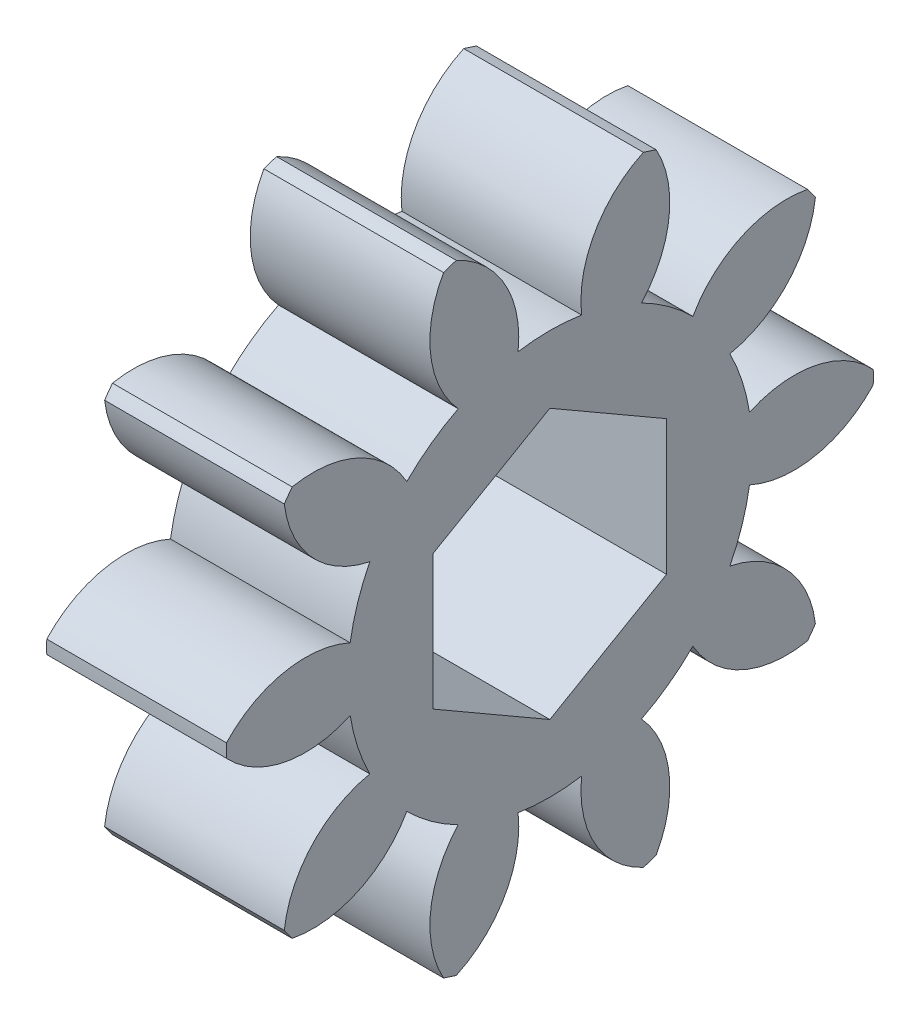
SolidWorks part; units mm, degrees
ref_plane "Plane1" through (0, 0, 0) normal (0, 0, 1) x (1, 0, 0)
ref_plane "Plane2" through (0, 0, 0) normal (0, 1, 0) x (1, 0, 0)
ref_plane "Plane3" through (0, 0, 0) normal (1, 0, 0) x (0, 0, -1)
sketch "HoldingSke" plane through (0, 0, 0) normal (0, 1, 0) x (1, 0, 0)
  line L0 (0, 0) -> (0.6565, -0.1158)
  line L1 (-15, 0) -> (100, 0) construction
  line L2 (0, 0) -> (-2.1039, 2.3779)
  line L3 (0, 0) -> (-11.863, 4.5341)
  line L4 (0, 0) -> (8.5048, 1.4996)
  line L5 (0, 0) -> (-46.8476, -17.4728)
  line L6 (0, 0) -> (-9.9476, -6.7116)
  line L7 (-2.1039, 2.3779) -> (8.6586, 51.2061)
  line L8 (-76.2, 54.61) -> (-75.3, 54.61)
  line L9 (-71.009, 38.7566) -> (-53.1078, 45.2721)
  line L10 (-76.2, 71.12) -> (104.1128, 71.12)
  line L11 (0, 0) -> (-12, 0)
  line L12 (-76.2, 101.6) -> (-76.147, 101.6)
  line L13 (24.9733, 27.94) -> (52.9518, 28.4284)
  line L14 (24.9733, 27.94) -> (24.9743, 27.94)
  line L15 (24.9733, 27.94) -> (100.4006, 29.5858)
  line L16 (-63.627, -1.5) -> (-12.827, -1.5)
  circle A0 centre (0, 0) radius 2.5
  circle A1 centre (0, 0) radius 5.624
  circle A2 centre (0, 0) radius 37.5
  circle A3 centre (0, 0) radius 2.5
  dimension "MHD" = 11.248
  dimension "Hub_dia" = 75
  dimension "Bore" = 5
  dimension "MBD" = 5
  dimension "Num_teeth" = 10
  dimension "Pitch" = 0.6667
  dimension "Overall_len" = 50
  dimension "Show_teeth" = 10
  dimension "Thickness" = 12
  dimension "OAL" = 50.0003
  dimension "T_dim" = 0.9
  dimension "Ap" = 20
  dimension "H" = 19.05
  dimension "Pitch_radius" = 180.3128
  dimension "Width" = 12
  dimension "Backlash" = 0.053
  dimension "Addendum_fac" = 1
  dimension "Dedendum_fac" = 1.25
  dimension "Clearance_fac" = 0.25
  dimension "Dedendum_add" = 0.001
  dimension "Module" = 1.5
sketch "BasProSke" plane through (0, 0, 0) normal (0, 1, 0) x (1, 0, 0)
  line L0 (-10, 0) -> (60, 0) construction
  line L1 (0, 0) -> (0, 9)
  line L2 (0, 0) -> (5, 0)
  line L3 (5, 0) -> (5, 9)
  line L4 (5, 9) -> (0, 9)
  dimension "Thickness" = 5
  dimension "Diameter" = 18
revolve "Base-Revolve" add sketch "BasProSke" angle 360 about L0
sketch "TooCutSke" plane through (0, 0, 0) normal (1, 0, 0) x (0, 0, -1)
  line L1 (0, 0) -> (0, 107) construction
  line L2 (0, 0) -> (-1.2658, 7.3924) construction
  line L3 (0, 0) -> (-4.5869, 14.117) construction
  line L4 (-1.2658, 7.3924) -> (-2.2934, 7.0585) construction
  arc A0 (0.8839, 5.5541) -> (-0.8839, 5.5541) centre (0, 0) ccw
  arc A1 (2.6378, 8.6313) -> (-2.6378, 8.6313) centre (0, 0) ccw
  circle A2 centre (0, 0) radius 7.5 construction
  circle A3 centre (0, 0) radius 7.0477 construction
  arc A4 (-0.8839, 5.5541) -> (-2.6378, 8.6313) centre (-3.8646, 5.8936) ccw
  arc A5 (2.6378, 8.6313) -> (0.8839, 5.5541) centre (3.8646, 5.8936) ccw
  dimension "Root_dia" = 11.248
  dimension "Overcut_dia" = 18.0508
  dimension "Pitch_dia" = 15
  dimension "Base_dia" = 14.0954
  dimension "Flank_rad" = 3
  dimension "Half_ang" = 18
  dimension "Half_CT" = 1.0805
extrude "ToothCut" cut sketch "TooCutSke" along normal through all
fillet "Breaks" [suppressed] radius 0.03
fillet "RootFillets" [suppressed] radius 0.376
pattern_circular "TeethCuts" count 10 every 36 about axis through (-10, 0, 0) along (1, 0, 0) of "ToothCut", "RootFillets", "Breaks"
sketch "HubNeaOneSke" plane through (0, 0, 0) normal (-1, 0, 0) x (0, 0, 1)
  circle A0 centre (0, 0) radius 5.624
  dimension "Diameter" = 11.248
extrude "HubNearOne" [suppressed] add sketch "HubNeaOneSke" along normal blind 45.0003
sketch "HubNeaBotSke" plane through (0, 0, 0) normal (-1, 0, 0) x (0, 0, 1)
  circle A0 centre (0, 0) radius 5.624
  dimension "Diameter" = 11.248
extrude "HubNearBoth" [suppressed] add sketch "HubNeaBotSke" along normal blind 22.5002
ref_plane "FarPln" through (5, 0, 0) normal (1, 0, 0) x (0, 0, -1)
sketch "HubFarSke" plane through (5, 0, 0) normal (1, 0, 0) x (0, 0, -1)
  circle A0 centre (0, 0) radius 5.624
  dimension "Diameter" = 11.248
extrude "HubFar" [suppressed] add sketch "HubFarSke" along normal blind 22.5002
sketch "BorSke" plane through (0, 0, 0) normal (1, 0, 0) x (0, 0, -1)
  line L1 (0, 3.75) -> (-3.2476, 1.875)
  line L2 (-3.2476, 1.875) -> (-3.2476, -1.875)
  line L3 (-3.2476, -1.875) -> (0, -3.75)
  line L4 (0, -3.75) -> (3.2476, -1.875)
  line L5 (3.2476, -1.875) -> (3.2476, 1.875)
  line L6 (3.2476, 1.875) -> (0, 3.75)
  circle A0 centre (0, 0) radius 3.75 construction
  circle A1 centre (0, 0) radius 3.2476 construction
  dimension "Diameter" = 7.5
extrude "Bore" cut sketch "BorSke" along normal mid plane 100.0006
sketch "KeySke" plane through (0, 0, 0) normal (1, 0, 0) x (0, 0, -1)
  line L0 (-1, 0) -> (-1, 3.4)
  line L1 (-1, 3.4) -> (1, 3.4)
  line L2 (1, 3.4) -> (1, 0)
  line L3 (0, 0) -> (0, 34) construction
  line L4 (-1, 0) -> (1, 0)
  dimension "Offset" = 3.4
  dimension "Width" = 2
extrude "Keyway" [suppressed] cut sketch "KeySke" along normal mid plane 100.0006
pattern_circular "Keyway2" [suppressed] count 2 every 90 about axis through (-10, 0, 0) along (1, 0, 0)
equation "' \"Module@HoldingSke\" = 6.35"
equation "' \"Num_teeth@HoldingSke\" = 12"
equation "' \"Ap@HoldingSke\" =  20"
equation "' \"Ap@HoldingSke\" = 20"
equation "' \"Width@HoldingSke\" = 0.5 * 25.4"
equation "' \"Hub_dia@HoldingSke\"= 1 * 25.4"
equation "' \"Hub_dia@HoldingSke\" = 1 * 25.4"
equation "' \"Overall_len@HoldingSke\" = 1.0 * 25.4"
equation "' \"Bore@HoldingSke\" = 0.75 * 25.4"
equation "' \"T_dim@HoldingSke\" = 0.1 * 25.4"
equation "' \"Width@KeySke\" = 0.25 * 25.4"
equation "' \"Show_teeth@HoldingSke\" = 13"
equation "' \"Backlash@HoldingSke\" = 0.009 * 25.4"
equation "' \"Addendum_fac@HoldingSke\" = 1.0"
equation "' \"Dedendum_fac@HoldingSke\" = 1.25"
equation "' \"Dedendum_add@HoldingSke\" = 0.00005 * 25.4"
equation "' \"Clearance_fac@HoldingSke\" = 0.25"
equation "\"Pitch@HoldingSke\" = 1 / \"Module@HoldingSke\""
equation "\"Overcut_dia@TooCutSke\" = (\"Num_teeth@HoldingSke\" + 2 * \"Addendum_fac@HoldingSke\") / \"Pitch@HoldingSke\" + 0.002 * 25.4"
equation "\"Pitch_dia@TooCutSke\" = \"Num_teeth@HoldingSke\" / \"Pitch@HoldingSke\""
equation "\"Base_dia@TooCutSke\" = \"Num_teeth@HoldingSke\" / \"Pitch@HoldingSke\" * cos((\"Ap@HoldingSke\"  * 3.14159265 / 180))"
equation "\"Root_dia@TooCutSke\" = (\"Num_teeth@HoldingSke\" + 2) / \"Pitch@HoldingSke\" - 2 * (\"Addendum_fac@HoldingSke\" + \"Dedendum_fac@HoldingSke\") / \"Pitch@HoldingSke\" - \"Dedendum_add@HoldingSke\" * 2"
equation "\"Half_ang@TooCutSke\" = 180 / \"Num_teeth@HoldingSke\""
equation "\"Half_CT@TooCutSke\" = \"Num_teeth@HoldingSke\" / \"Pitch@HoldingSke\" * sin((3.14159265 / 2 / \"Num_teeth@HoldingSke\")) / 2 - 7 * \"Backlash@HoldingSke\" / 4"
equation "\"Flank_rad@TooCutSke\" = \"Num_teeth@HoldingSke\" / \"Pitch@HoldingSke\" / 5"
equation "\"Radius@RootFillets\" = \"Clearance_fac@HoldingSke\" / \"Pitch@HoldingSke\" + \"Dedendum_add@HoldingSke\""
equation "\"Break_rad@Breaks\" = 0.02 / \"Pitch@HoldingSke\""
equation "\"Thickness@HoldingSke\" = \"Width@HoldingSke\""
equation "\"OAL@HoldingSke\" = \"Thickness@HoldingSke\""
equation "\"MHD@HoldingSke\" = (\"Num_teeth@HoldingSke\" + 2) / \"Pitch@HoldingSke\" - 2 * (\"Addendum_fac@HoldingSke\" + \"Dedendum_fac@HoldingSke\")  / \"Pitch@HoldingSke\" - \"Dedendum_add@HoldingSke\" * 2"
equation "\"MBD@HoldingSke\" = (\"Num_teeth@HoldingSke\" + 2) / \"Pitch@HoldingSke\" - 2 * (\"Addendum_fac@HoldingSke\" + \"Dedendum_fac@HoldingSke\")  / \"Pitch@HoldingSke\" - \"Dedendum_add@HoldingSke\" * 2 - 0.002 * 25.4"
equation "\"MHD@HoldingSke\" = ((sgn( \"MHD@HoldingSke\" - \"Hub_dia@HoldingSke\" )-1)*( \"MHD@HoldingSke\" - \"Hub_dia@HoldingSke\" ))/-2+ \"Hub_dia@HoldingSke\""
equation "\"MBD@HoldingSke\" = ((sgn( \"MBD@HoldingSke\" - \"Bore@HoldingSke\" )-1)*( \"MBD@HoldingSke\" - \"Bore@HoldingSke\" ))/-2+ \"Bore@HoldingSke\""
equation "\"OAL@HoldingSke\" = ((sgn( \"OAL@HoldingSke\" - \"Overall_len@HoldingSke\" )+1)*( \"OAL@HoldingSke\" - \"Overall_len@HoldingSke\" ))/2 + \"Overall_len@HoldingSke\" + 0.000002 * 25.4"
equation "\"Num_teeth@TeethCuts\" = int( \"Show_teeth@HoldingSke\" ) + 1"
equation "\"Num_teeth@TeethCuts\" = ((sgn( \"Num_teeth@TeethCuts\" - \"Num_teeth@HoldingSke\" )-1)*( \"Num_teeth@TeethCuts\" - \"Num_teeth@HoldingSke\" ))/-2+ \"Num_teeth@HoldingSke\""
equation "\"Num_teeth@TeethCuts\" = ((sgn( \"Num_teeth@TeethCuts\" - 2.0)+1)*( \"Num_teeth@TeethCuts\" - 2.0))/2 +2.0"
equation "\"Angle@TeethCuts\" = 360.0 / \"Num_teeth@HoldingSke\""
equation "\"Diameter@BasProSke\" = (\"Num_teeth@HoldingSke\" + 2 * \"Addendum_fac@HoldingSke\") / \"Pitch@HoldingSke\""
equation "' \"Fillet_rad@BasProSke\" =  \"Thickness@HoldingSke\" * 0.05"
equation "' \"Fillet_rad@BasProSke\" = \"Thickness@HoldingSke\" * 0.05"
equation "\"MHD@HoldingSke\" = ((sgn( \"MHD@HoldingSke\" - \"Root_dia@TooCutSke\" )-1)*( \"MHD@HoldingSke\" - \"Root_dia@TooCutSke\" ))/-2+ \"Root_dia@TooCutSke\""
equation "\"Diameter@HubNeaOneSke\" = \"MHD@HoldingSke\""
equation "\"Length@HubNearOne\" = \"OAL@HoldingSke\" - \"Thickness@BasProSke\""
equation "\"Diameter@HubNeaBotSke\" = \"MHD@HoldingSke\""
equation "\"Length@HubNearBoth\" = ( \"OAL@HoldingSke\" - \"Thickness@BasProSke\" ) / 2.0"
equation "\"Thickness@FarPln\" = \"Thickness@BasProSke\""
equation "\"Diameter@HubFarSke\" = \"MHD@HoldingSke\""
equation "\"Length@HubFar\" = ( \"OAL@HoldingSke\" - \"Thickness@BasProSke\" ) / 2.0"
equation "\"Diameter@BorSke\"=7.5"
equation "\"D1@Bore\" = \"OAL@HoldingSke\" * 2.0"
equation "\"D1@Keyway\" = \"OAL@HoldingSke\" * 2.0"
equation "\"Offset@KeySke\" = \"T_dim@HoldingSke\" + \"MBD@HoldingSke\" / 2.0"
